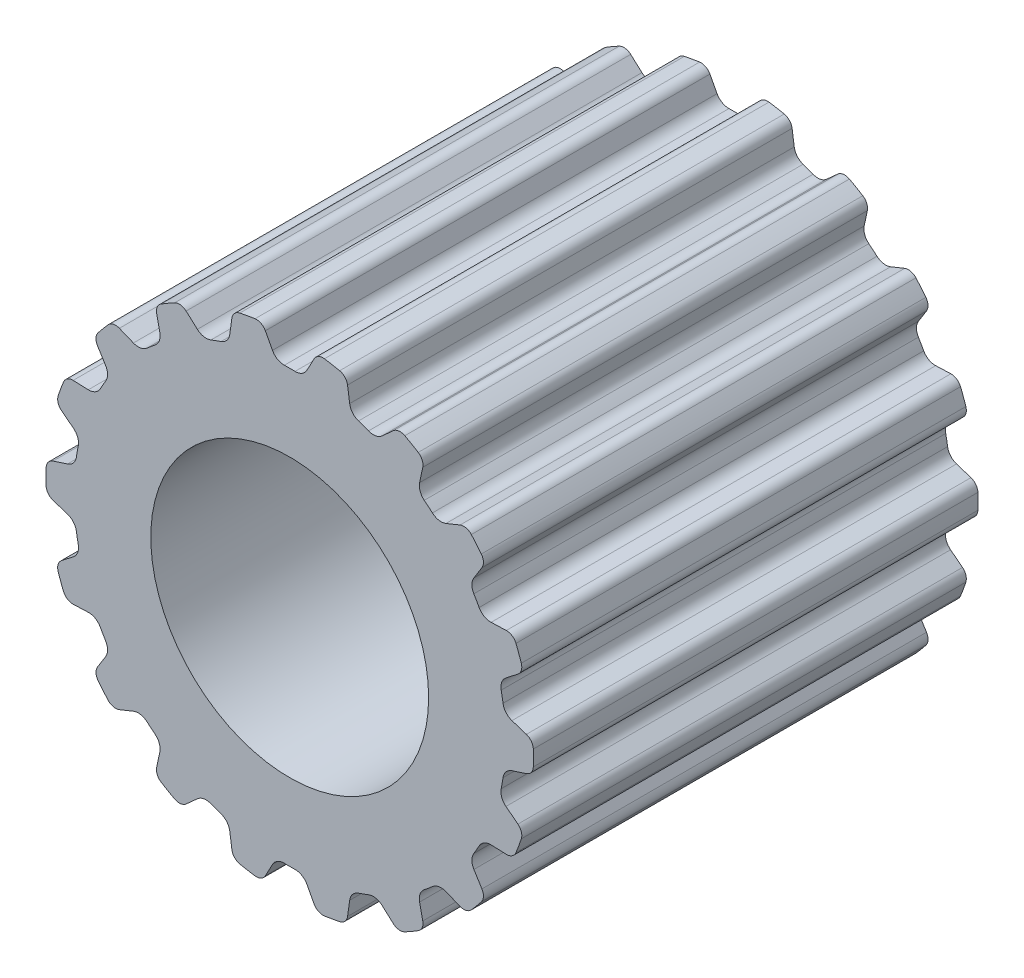
SolidWorks part; units mm, degrees
ref_plane "Front Plane" through (0, 0, 0) normal (0, 0, 1) x (1, 0, 0)
ref_plane "Top Plane" through (0, 0, 0) normal (0, 1, 0) x (1, 0, 0)
ref_plane "Right Plane" through (0, 0, 0) normal (1, 0, 0) x (0, 0, -1)
sketch "Sketch1" plane through (0, 0, 0) normal (0, 0, 1) x (1, 0, 0)
  circle A0 centre (0, 0) radius 5.57
  dimension "OD" = 11.14
sketch "PITCH DIAMETER" plane through (0, 0, 0) normal (0, 0, 1) x (1, 0, 0)
  circle A0 centre (0, 0) radius 5.82
  dimension "PD" = 11.64
extrude "Boss-Extrude1" add sketch "Sketch1" along normal mid plane 10.16
sketch "Sketch2" plane through (0, 0, 5.08) normal (0, 0, 1) x (1, 0, 0)
  line L0 (0.305, 4.9206) -> (0.6312, 5.5341)
  line L1 (-0.305, 4.9206) -> (-0.6312, 5.5341)
  arc A0 (0.305, 4.9206) -> (-0.305, 4.9206) centre (0, 0) ccw
  circle A1 centre (0, 0) radius 5.57 construction
  arc A2 (-0.6312, 5.5341) -> (0.6312, 5.5341) centre (0, 0) cw
  dimension "D2" = 0.64
  dimension "Angle" = 56
  dimension "width" = 0.61
extrude "Cut-Extrude1" cut sketch "Sketch2" against normal through all
fillet "Fillet1" radius 0.23 2 edges at (0.6312, 5.5341, 0) (-0.6312, 5.5341, 0)
fillet "Fillet2" radius 0.3 2 edges at (0.305, 4.9206, 0) (-0.305, 4.9206, 0)
pattern_circular "CirPattern1" count 18 over 360 about axis through (0, 0, 0) along (0, 0, 1) of "Cut-Extrude1", "Fillet1", "Fillet2"
sketch "Sketch3" plane through (0, 0, 5.08) normal (0, 0, 1) x (1, 0, 0)
  circle A0 centre (0, 0) radius 3.175
  dimension "D1" = 6.35
extrude "Cut-Extrude2" cut sketch "Sketch3" against normal through all
sketch "Sketch4" plane through (0, 0, 5.08) normal (0, 0, 1) x (1, 0, 0)
  line L0 (-5.2151, -1.4847) -> (-4.9419, -1.2713)
  line L1 (-5.2151, -1.4847) -> (-4.9419, -1.2713)
  line L2 (-5.0787, -0.4956) -> (-5.4084, -0.3885)
  line L3 (-5.0787, -0.4956) -> (-5.4084, -0.3885)
  line L4 (-5.4084, 0.3885) -> (-5.0787, 0.4956)
  line L5 (-5.4084, 0.3885) -> (-5.0787, 0.4956)
  line L6 (-4.9419, 1.2713) -> (-5.2151, 1.4847)
  line L7 (-4.9419, 1.2713) -> (-5.2151, 1.4847)
  line L8 (-4.9493, 2.2148) -> (-4.6029, 2.2027)
  line L9 (-4.9493, 2.2148) -> (-4.6029, 2.2027)
  line L10 (-4.2091, 2.8848) -> (-4.3928, 3.1788)
  line L11 (-4.2091, 2.8848) -> (-4.3928, 3.1788)
  line L12 (-3.8933, 3.774) -> (-3.5719, 3.6442)
  line L13 (-3.8933, 3.774) -> (-3.5719, 3.6442)
  line L14 (-2.9686, 4.1504) -> (-3.0406, 4.4895)
  line L15 (-2.9686, 4.1504) -> (-3.0406, 4.4895)
  line L16 (-2.3677, 4.878) -> (-2.1101, 4.6461)
  line L17 (-2.3677, 4.878) -> (-2.1101, 4.6461)
  line L18 (-1.37, 4.9154) -> (-1.3217, 5.2587)
  line L19 (-1.37, 4.9154) -> (-1.3217, 5.2587)
  line L20 (-0.5566, 5.3937) -> (-0.3938, 5.0876)
  line L21 (-0.5566, 5.3937) -> (-0.3938, 5.0876)
  line L22 (0.3938, 5.0876) -> (0.5566, 5.3937)
  line L23 (0.3938, 5.0876) -> (0.5566, 5.3937)
  line L24 (1.3217, 5.2587) -> (1.37, 4.9154)
  line L25 (1.3217, 5.2587) -> (1.37, 4.9154)
  line L26 (2.1101, 4.6461) -> (2.3677, 4.878)
  line L27 (2.1101, 4.6461) -> (2.3677, 4.878)
  line L28 (3.0406, 4.4895) -> (2.9686, 4.1504)
  line L29 (3.0406, 4.4895) -> (2.9686, 4.1504)
  line L30 (3.5719, 3.6442) -> (3.8933, 3.774)
  line L31 (3.5719, 3.6442) -> (3.8933, 3.774)
  line L32 (4.3928, 3.1788) -> (4.2091, 2.8848)
  line L33 (4.3928, 3.1788) -> (4.2091, 2.8848)
  line L34 (4.6029, 2.2027) -> (4.9493, 2.2148)
  line L35 (4.6029, 2.2027) -> (4.9493, 2.2148)
  line L36 (5.2151, 1.4847) -> (4.9419, 1.2713)
  line L37 (5.2151, 1.4847) -> (4.9419, 1.2713)
  line L38 (5.0787, 0.4956) -> (5.4084, 0.3885)
  line L39 (5.0787, 0.4956) -> (5.4084, 0.3885)
  line L40 (5.4084, -0.3885) -> (5.0787, -0.4956)
  line L41 (5.4084, -0.3885) -> (5.0787, -0.4956)
  line L42 (4.9419, -1.2713) -> (5.2151, -1.4847)
  line L43 (4.9419, -1.2713) -> (5.2151, -1.4847)
  line L44 (4.9493, -2.2148) -> (4.6029, -2.2027)
  line L45 (4.9493, -2.2148) -> (4.6029, -2.2027)
  line L46 (4.2091, -2.8848) -> (4.3928, -3.1788)
  line L47 (4.2091, -2.8848) -> (4.3928, -3.1788)
  line L48 (3.8933, -3.774) -> (3.5719, -3.6442)
  line L49 (3.8933, -3.774) -> (3.5719, -3.6442)
  line L50 (2.9686, -4.1504) -> (3.0406, -4.4895)
  line L51 (2.9686, -4.1504) -> (3.0406, -4.4895)
  line L52 (2.3677, -4.878) -> (2.1101, -4.6461)
  line L53 (2.3677, -4.878) -> (2.1101, -4.6461)
  line L54 (1.37, -4.9154) -> (1.3217, -5.2587)
  line L55 (1.37, -4.9154) -> (1.3217, -5.2587)
  line L56 (0.5566, -5.3937) -> (0.3938, -5.0876)
  line L57 (0.5566, -5.3937) -> (0.3938, -5.0876)
  line L58 (-0.3938, -5.0876) -> (-0.5566, -5.3937)
  line L59 (-0.3938, -5.0876) -> (-0.5566, -5.3937)
  line L60 (-1.3217, -5.2587) -> (-1.37, -4.9154)
  line L61 (-1.3217, -5.2587) -> (-1.37, -4.9154)
  line L62 (-2.1101, -4.6461) -> (-2.3677, -4.878)
  line L63 (-2.1101, -4.6461) -> (-2.3677, -4.878)
  line L64 (-3.0406, -4.4895) -> (-2.9686, -4.1504)
  line L65 (-3.0406, -4.4895) -> (-2.9686, -4.1504)
  line L66 (-3.5719, -3.6442) -> (-3.8933, -3.774)
  line L67 (-3.5719, -3.6442) -> (-3.8933, -3.774)
  line L68 (-4.3928, -3.1788) -> (-4.2091, -2.8848)
  line L69 (-4.3928, -3.1788) -> (-4.2091, -2.8848)
  line L70 (-4.6029, -2.2027) -> (-4.9493, -2.2148)
  line L71 (-4.6029, -2.2027) -> (-4.9493, -2.2148)
  arc A0 (-5.292, -1.7377) -> (-5.1709, -2.0705) centre (0, 0) ccw
  arc A1 (-5.292, -1.7377) -> (-5.1709, -2.0705) centre (0, 0) ccw
  arc A2 (-5.2151, -1.4847) -> (-5.292, -1.7377) centre (-5.0735, -1.666) ccw
  arc A3 (-5.2151, -1.4847) -> (-5.292, -1.7377) centre (-5.0735, -1.666) ccw
  arc A4 (-4.9419, -1.2713) -> (-4.8325, -0.9755) centre (-5.1266, -1.0349) ccw
  arc A5 (-4.9419, -1.2713) -> (-4.8325, -0.9755) centre (-5.1266, -1.0349) ccw
  arc A6 (-4.8747, -0.7361) -> (-4.8325, -0.9755) centre (0, 0) ccw
  arc A7 (-4.8747, -0.7361) -> (-4.8325, -0.9755) centre (0, 0) ccw
  arc A8 (-4.8747, -0.7361) -> (-5.0787, -0.4956) centre (-5.1714, -0.7809) ccw
  arc A9 (-4.8747, -0.7361) -> (-5.0787, -0.4956) centre (-5.1714, -0.7809) ccw
  arc A10 (-5.5672, -0.1771) -> (-5.4084, -0.3885) centre (-5.3373, -0.1698) ccw
  arc A11 (-5.5672, -0.1771) -> (-5.4084, -0.3885) centre (-5.3373, -0.1698) ccw
  arc A12 (-5.5672, 0.1771) -> (-5.5672, -0.1771) centre (0, 0) ccw
  arc A13 (-5.5672, 0.1771) -> (-5.5672, -0.1771) centre (0, 0) ccw
  arc A14 (-5.4084, 0.3885) -> (-5.5672, 0.1771) centre (-5.3373, 0.1698) ccw
  arc A15 (-5.4084, 0.3885) -> (-5.5672, 0.1771) centre (-5.3373, 0.1698) ccw
  arc A16 (-5.0787, 0.4956) -> (-4.8747, 0.7361) centre (-5.1714, 0.7809) ccw
  arc A17 (-5.0787, 0.4956) -> (-4.8747, 0.7361) centre (-5.1714, 0.7809) ccw
  arc A18 (-4.8325, 0.9755) -> (-4.8747, 0.7361) centre (0, 0) ccw
  arc A19 (-4.8325, 0.9755) -> (-4.8747, 0.7361) centre (0, 0) ccw
  arc A20 (-4.8325, 0.9755) -> (-4.9419, 1.2713) centre (-5.1266, 1.0349) ccw
  arc A21 (-4.8325, 0.9755) -> (-4.9419, 1.2713) centre (-5.1266, 1.0349) ccw
  arc A22 (-5.292, 1.7377) -> (-5.2151, 1.4847) centre (-5.0735, 1.666) ccw
  arc A23 (-5.292, 1.7377) -> (-5.2151, 1.4847) centre (-5.0735, 1.666) ccw
  arc A24 (-5.1709, 2.0705) -> (-5.292, 1.7377) centre (0, 0) ccw
  arc A25 (-5.1709, 2.0705) -> (-5.292, 1.7377) centre (0, 0) ccw
  arc A26 (-4.9493, 2.2148) -> (-5.1709, 2.0705) centre (-4.9574, 1.985) ccw
  arc A27 (-4.9493, 2.2148) -> (-5.1709, 2.0705) centre (-4.9574, 1.985) ccw
  arc A28 (-4.6029, 2.2027) -> (-4.329, 2.359) centre (-4.5924, 2.5026) ccw
  arc A29 (-4.6029, 2.2027) -> (-4.329, 2.359) centre (-4.5924, 2.5026) ccw
  arc A30 (-4.2074, 2.5695) -> (-4.329, 2.359) centre (0, 0) ccw
  arc A31 (-4.2074, 2.5695) -> (-4.329, 2.359) centre (0, 0) ccw
  arc A32 (-4.2074, 2.5695) -> (-4.2091, 2.8848) centre (-4.4635, 2.7259) ccw
  arc A33 (-4.2074, 2.5695) -> (-4.2091, 2.8848) centre (-4.4635, 2.7259) ccw
  arc A34 (-4.3785, 3.4429) -> (-4.3928, 3.1788) centre (-4.1977, 3.3007) ccw
  arc A35 (-4.3785, 3.4429) -> (-4.3928, 3.1788) centre (-4.1977, 3.3007) ccw
  arc A36 (-4.1509, 3.7142) -> (-4.3785, 3.4429) centre (0, 0) ccw
  arc A37 (-4.1509, 3.7142) -> (-4.3785, 3.4429) centre (0, 0) ccw
  arc A38 (-3.8933, 3.774) -> (-4.1509, 3.7142) centre (-3.9795, 3.5608) ccw
  arc A39 (-3.8933, 3.774) -> (-4.1509, 3.7142) centre (-3.9795, 3.5608) ccw
  arc A40 (-3.5719, 3.6442) -> (-3.2611, 3.6973) centre (-3.4595, 3.9223) ccw
  arc A41 (-3.5719, 3.6442) -> (-3.2611, 3.6973) centre (-3.4595, 3.9223) ccw
  arc A42 (-3.0749, 3.8536) -> (-3.2611, 3.6973) centre (0, 0) ccw
  arc A43 (-3.0749, 3.8536) -> (-3.2611, 3.6973) centre (0, 0) ccw
  arc A44 (-3.0749, 3.8536) -> (-2.9686, 4.1504) centre (-3.262, 4.0881) ccw
  arc A45 (-3.0749, 3.8536) -> (-2.9686, 4.1504) centre (-3.262, 4.0881) ccw
  arc A46 (-2.9369, 4.7328) -> (-3.0406, 4.4895) centre (-2.8157, 4.5374) ccw
  arc A47 (-2.9369, 4.7328) -> (-3.0406, 4.4895) centre (-2.8157, 4.5374) ccw
  arc A48 (-2.6303, 4.9099) -> (-2.9369, 4.7328) centre (0, 0) ccw
  arc A49 (-2.6303, 4.9099) -> (-2.9369, 4.7328) centre (0, 0) ccw
  arc A50 (-2.3677, 4.878) -> (-2.6303, 4.9099) centre (-2.5216, 4.7071) ccw
  arc A51 (-2.3677, 4.878) -> (-2.6303, 4.9099) centre (-2.5216, 4.7071) ccw
  arc A52 (-2.1101, 4.6461) -> (-1.7998, 4.5897) centre (-1.9094, 4.869) ccw
  arc A53 (-2.1101, 4.6461) -> (-1.7998, 4.5897) centre (-1.9094, 4.869) ccw
  arc A54 (-1.5714, 4.6728) -> (-1.7998, 4.5897) centre (0, 0) ccw
  arc A55 (-1.5714, 4.6728) -> (-1.7998, 4.5897) centre (0, 0) ccw
  arc A56 (-1.5714, 4.6728) -> (-1.37, 4.9154) centre (-1.6671, 4.9572) ccw
  arc A57 (-1.5714, 4.6728) -> (-1.37, 4.9154) centre (-1.6671, 4.9572) ccw
  arc A58 (-1.1411, 5.4519) -> (-1.3217, 5.2587) centre (-1.094, 5.2267) ccw
  arc A59 (-1.1411, 5.4519) -> (-1.3217, 5.2587) centre (-1.094, 5.2267) ccw
  arc A60 (-0.7924, 5.5134) -> (-1.1411, 5.4519) centre (0, 0) ccw
  arc A61 (-0.7924, 5.5134) -> (-1.1411, 5.4519) centre (0, 0) ccw
  arc A62 (-0.5566, 5.3937) -> (-0.7924, 5.5134) centre (-0.7596, 5.2857) ccw
  arc A63 (-0.5566, 5.3937) -> (-0.7924, 5.5134) centre (-0.7596, 5.2857) ccw
  arc A64 (-0.3938, 5.0876) -> (-0.1215, 4.9285) centre (-0.1289, 5.2284) ccw
  arc A65 (-0.3938, 5.0876) -> (-0.1215, 4.9285) centre (-0.1289, 5.2284) ccw
  arc A66 (0.1215, 4.9285) -> (-0.1215, 4.9285) centre (0, 0) ccw
  arc A67 (0.1215, 4.9285) -> (-0.1215, 4.9285) centre (0, 0) ccw
  arc A68 (0.1215, 4.9285) -> (0.3938, 5.0876) centre (0.1289, 5.2284) ccw
  arc A69 (0.1215, 4.9285) -> (0.3938, 5.0876) centre (0.1289, 5.2284) ccw
  arc A70 (0.7924, 5.5134) -> (0.5566, 5.3937) centre (0.7596, 5.2857) ccw
  arc A71 (0.7924, 5.5134) -> (0.5566, 5.3937) centre (0.7596, 5.2857) ccw
  arc A72 (1.1411, 5.4519) -> (0.7924, 5.5134) centre (0, 0) ccw
  arc A73 (1.1411, 5.4519) -> (0.7924, 5.5134) centre (0, 0) ccw
  arc A74 (1.3217, 5.2587) -> (1.1411, 5.4519) centre (1.094, 5.2267) ccw
  arc A75 (1.3217, 5.2587) -> (1.1411, 5.4519) centre (1.094, 5.2267) ccw
  arc A76 (1.37, 4.9154) -> (1.5714, 4.6728) centre (1.6671, 4.9572) ccw
  arc A77 (1.37, 4.9154) -> (1.5714, 4.6728) centre (1.6671, 4.9572) ccw
  arc A78 (1.7998, 4.5897) -> (1.5714, 4.6728) centre (0, 0) ccw
  arc A79 (1.7998, 4.5897) -> (1.5714, 4.6728) centre (0, 0) ccw
  arc A80 (1.7998, 4.5897) -> (2.1101, 4.6461) centre (1.9094, 4.869) ccw
  arc A81 (1.7998, 4.5897) -> (2.1101, 4.6461) centre (1.9094, 4.869) ccw
  arc A82 (2.6303, 4.9099) -> (2.3677, 4.878) centre (2.5216, 4.7071) ccw
  arc A83 (2.6303, 4.9099) -> (2.3677, 4.878) centre (2.5216, 4.7071) ccw
  arc A84 (2.9369, 4.7328) -> (2.6303, 4.9099) centre (0, 0) ccw
  arc A85 (2.9369, 4.7328) -> (2.6303, 4.9099) centre (0, 0) ccw
  arc A86 (3.0406, 4.4895) -> (2.9369, 4.7328) centre (2.8157, 4.5374) ccw
  arc A87 (3.0406, 4.4895) -> (2.9369, 4.7328) centre (2.8157, 4.5374) ccw
  arc A88 (2.9686, 4.1504) -> (3.0749, 3.8536) centre (3.262, 4.0881) ccw
  arc A89 (2.9686, 4.1504) -> (3.0749, 3.8536) centre (3.262, 4.0881) ccw
  arc A90 (3.2611, 3.6973) -> (3.0749, 3.8536) centre (0, 0) ccw
  arc A91 (3.2611, 3.6973) -> (3.0749, 3.8536) centre (0, 0) ccw
  arc A92 (3.2611, 3.6973) -> (3.5719, 3.6442) centre (3.4595, 3.9223) ccw
  arc A93 (3.2611, 3.6973) -> (3.5719, 3.6442) centre (3.4595, 3.9223) ccw
  arc A94 (4.1509, 3.7142) -> (3.8933, 3.774) centre (3.9795, 3.5608) ccw
  arc A95 (4.1509, 3.7142) -> (3.8933, 3.774) centre (3.9795, 3.5608) ccw
  arc A96 (4.3785, 3.4429) -> (4.1509, 3.7142) centre (0, 0) ccw
  arc A97 (4.3785, 3.4429) -> (4.1509, 3.7142) centre (0, 0) ccw
  arc A98 (4.3928, 3.1788) -> (4.3785, 3.4429) centre (4.1977, 3.3007) ccw
  arc A99 (4.3928, 3.1788) -> (4.3785, 3.4429) centre (4.1977, 3.3007) ccw
  arc A100 (4.2091, 2.8848) -> (4.2074, 2.5695) centre (4.4635, 2.7259) ccw
  arc A101 (4.2091, 2.8848) -> (4.2074, 2.5695) centre (4.4635, 2.7259) ccw
  arc A102 (4.329, 2.359) -> (4.2074, 2.5695) centre (0, 0) ccw
  arc A103 (4.329, 2.359) -> (4.2074, 2.5695) centre (0, 0) ccw
  arc A104 (4.329, 2.359) -> (4.6029, 2.2027) centre (4.5924, 2.5026) ccw
  arc A105 (4.329, 2.359) -> (4.6029, 2.2027) centre (4.5924, 2.5026) ccw
  arc A106 (5.1709, 2.0705) -> (4.9493, 2.2148) centre (4.9574, 1.985) ccw
  arc A107 (5.1709, 2.0705) -> (4.9493, 2.2148) centre (4.9574, 1.985) ccw
  arc A108 (5.292, 1.7377) -> (5.1709, 2.0705) centre (0, 0) ccw
  arc A109 (5.292, 1.7377) -> (5.1709, 2.0705) centre (0, 0) ccw
  arc A110 (5.2151, 1.4847) -> (5.292, 1.7377) centre (5.0735, 1.666) ccw
  arc A111 (5.2151, 1.4847) -> (5.292, 1.7377) centre (5.0735, 1.666) ccw
  arc A112 (4.9419, 1.2713) -> (4.8325, 0.9755) centre (5.1266, 1.0349) ccw
  arc A113 (4.9419, 1.2713) -> (4.8325, 0.9755) centre (5.1266, 1.0349) ccw
  arc A114 (4.8747, 0.7361) -> (4.8325, 0.9755) centre (0, 0) ccw
  arc A115 (4.8747, 0.7361) -> (4.8325, 0.9755) centre (0, 0) ccw
  arc A116 (4.8747, 0.7361) -> (5.0787, 0.4956) centre (5.1714, 0.7809) ccw
  arc A117 (4.8747, 0.7361) -> (5.0787, 0.4956) centre (5.1714, 0.7809) ccw
  arc A118 (5.5672, 0.1771) -> (5.4084, 0.3885) centre (5.3373, 0.1698) ccw
  arc A119 (5.5672, 0.1771) -> (5.4084, 0.3885) centre (5.3373, 0.1698) ccw
  arc A120 (5.5672, -0.1771) -> (5.5672, 0.1771) centre (0, 0) ccw
  arc A121 (5.5672, -0.1771) -> (5.5672, 0.1771) centre (0, 0) ccw
  arc A122 (5.4084, -0.3885) -> (5.5672, -0.1771) centre (5.3373, -0.1698) ccw
  arc A123 (5.4084, -0.3885) -> (5.5672, -0.1771) centre (5.3373, -0.1698) ccw
  arc A124 (5.0787, -0.4956) -> (4.8747, -0.7361) centre (5.1714, -0.7809) ccw
  arc A125 (5.0787, -0.4956) -> (4.8747, -0.7361) centre (5.1714, -0.7809) ccw
  arc A126 (4.8325, -0.9755) -> (4.8747, -0.7361) centre (0, 0) ccw
  arc A127 (4.8325, -0.9755) -> (4.8747, -0.7361) centre (0, 0) ccw
  arc A128 (4.8325, -0.9755) -> (4.9419, -1.2713) centre (5.1266, -1.0349) ccw
  arc A129 (4.8325, -0.9755) -> (4.9419, -1.2713) centre (5.1266, -1.0349) ccw
  arc A130 (5.292, -1.7377) -> (5.2151, -1.4847) centre (5.0735, -1.666) ccw
  arc A131 (5.292, -1.7377) -> (5.2151, -1.4847) centre (5.0735, -1.666) ccw
  arc A132 (5.1709, -2.0705) -> (5.292, -1.7377) centre (0, 0) ccw
  arc A133 (5.1709, -2.0705) -> (5.292, -1.7377) centre (0, 0) ccw
  arc A134 (4.9493, -2.2148) -> (5.1709, -2.0705) centre (4.9574, -1.985) ccw
  arc A135 (4.9493, -2.2148) -> (5.1709, -2.0705) centre (4.9574, -1.985) ccw
  arc A136 (4.6029, -2.2027) -> (4.329, -2.359) centre (4.5924, -2.5026) ccw
  arc A137 (4.6029, -2.2027) -> (4.329, -2.359) centre (4.5924, -2.5026) ccw
  arc A138 (4.2074, -2.5695) -> (4.329, -2.359) centre (0, 0) ccw
  arc A139 (4.2074, -2.5695) -> (4.329, -2.359) centre (0, 0) ccw
  arc A140 (4.2074, -2.5695) -> (4.2091, -2.8848) centre (4.4635, -2.7259) ccw
  arc A141 (4.2074, -2.5695) -> (4.2091, -2.8848) centre (4.4635, -2.7259) ccw
  arc A142 (4.3785, -3.4429) -> (4.3928, -3.1788) centre (4.1977, -3.3007) ccw
  arc A143 (4.3785, -3.4429) -> (4.3928, -3.1788) centre (4.1977, -3.3007) ccw
  arc A144 (4.1509, -3.7142) -> (4.3785, -3.4429) centre (0, 0) ccw
  arc A145 (4.1509, -3.7142) -> (4.3785, -3.4429) centre (0, 0) ccw
  arc A146 (3.8933, -3.774) -> (4.1509, -3.7142) centre (3.9795, -3.5608) ccw
  arc A147 (3.8933, -3.774) -> (4.1509, -3.7142) centre (3.9795, -3.5608) ccw
  arc A148 (3.5719, -3.6442) -> (3.2611, -3.6973) centre (3.4595, -3.9223) ccw
  arc A149 (3.5719, -3.6442) -> (3.2611, -3.6973) centre (3.4595, -3.9223) ccw
  arc A150 (3.0749, -3.8536) -> (3.2611, -3.6973) centre (0, 0) ccw
  arc A151 (3.0749, -3.8536) -> (3.2611, -3.6973) centre (0, 0) ccw
  arc A152 (3.0749, -3.8536) -> (2.9686, -4.1504) centre (3.262, -4.0881) ccw
  arc A153 (3.0749, -3.8536) -> (2.9686, -4.1504) centre (3.262, -4.0881) ccw
  arc A154 (2.9369, -4.7328) -> (3.0406, -4.4895) centre (2.8157, -4.5374) ccw
  arc A155 (2.9369, -4.7328) -> (3.0406, -4.4895) centre (2.8157, -4.5374) ccw
  arc A156 (2.6303, -4.9099) -> (2.9369, -4.7328) centre (0, 0) ccw
  arc A157 (2.6303, -4.9099) -> (2.9369, -4.7328) centre (0, 0) ccw
  arc A158 (2.3677, -4.878) -> (2.6303, -4.9099) centre (2.5216, -4.7071) ccw
  arc A159 (2.3677, -4.878) -> (2.6303, -4.9099) centre (2.5216, -4.7071) ccw
  arc A160 (2.1101, -4.6461) -> (1.7998, -4.5897) centre (1.9094, -4.869) ccw
  arc A161 (2.1101, -4.6461) -> (1.7998, -4.5897) centre (1.9094, -4.869) ccw
  arc A162 (1.5714, -4.6728) -> (1.7998, -4.5897) centre (0, 0) ccw
  arc A163 (1.5714, -4.6728) -> (1.7998, -4.5897) centre (0, 0) ccw
  arc A164 (1.5714, -4.6728) -> (1.37, -4.9154) centre (1.6671, -4.9572) ccw
  arc A165 (1.5714, -4.6728) -> (1.37, -4.9154) centre (1.6671, -4.9572) ccw
  arc A166 (1.1411, -5.4519) -> (1.3217, -5.2587) centre (1.094, -5.2267) ccw
  arc A167 (1.1411, -5.4519) -> (1.3217, -5.2587) centre (1.094, -5.2267) ccw
  arc A168 (0.7924, -5.5134) -> (1.1411, -5.4519) centre (0, 0) ccw
  arc A169 (0.7924, -5.5134) -> (1.1411, -5.4519) centre (0, 0) ccw
  arc A170 (0.5566, -5.3937) -> (0.7924, -5.5134) centre (0.7596, -5.2857) ccw
  arc A171 (0.5566, -5.3937) -> (0.7924, -5.5134) centre (0.7596, -5.2857) ccw
  arc A172 (0.3938, -5.0876) -> (0.1215, -4.9285) centre (0.1289, -5.2284) ccw
  arc A173 (0.3938, -5.0876) -> (0.1215, -4.9285) centre (0.1289, -5.2284) ccw
  arc A174 (-0.1215, -4.9285) -> (0.1215, -4.9285) centre (0, 0) ccw
  arc A175 (-0.1215, -4.9285) -> (0.1215, -4.9285) centre (0, 0) ccw
  arc A176 (-0.1215, -4.9285) -> (-0.3938, -5.0876) centre (-0.1289, -5.2284) ccw
  arc A177 (-0.1215, -4.9285) -> (-0.3938, -5.0876) centre (-0.1289, -5.2284) ccw
  arc A178 (-0.7924, -5.5134) -> (-0.5566, -5.3937) centre (-0.7596, -5.2857) ccw
  arc A179 (-0.7924, -5.5134) -> (-0.5566, -5.3937) centre (-0.7596, -5.2857) ccw
  arc A180 (-1.1411, -5.4519) -> (-0.7924, -5.5134) centre (0, 0) ccw
  arc A181 (-1.1411, -5.4519) -> (-0.7924, -5.5134) centre (0, 0) ccw
  arc A182 (-1.3217, -5.2587) -> (-1.1411, -5.4519) centre (-1.094, -5.2267) ccw
  arc A183 (-1.3217, -5.2587) -> (-1.1411, -5.4519) centre (-1.094, -5.2267) ccw
  arc A184 (-1.37, -4.9154) -> (-1.5714, -4.6728) centre (-1.6671, -4.9572) ccw
  arc A185 (-1.37, -4.9154) -> (-1.5714, -4.6728) centre (-1.6671, -4.9572) ccw
  arc A186 (-1.7998, -4.5897) -> (-1.5714, -4.6728) centre (0, 0) ccw
  arc A187 (-1.7998, -4.5897) -> (-1.5714, -4.6728) centre (0, 0) ccw
  arc A188 (-1.7998, -4.5897) -> (-2.1101, -4.6461) centre (-1.9094, -4.869) ccw
  arc A189 (-1.7998, -4.5897) -> (-2.1101, -4.6461) centre (-1.9094, -4.869) ccw
  arc A190 (-2.6303, -4.9099) -> (-2.3677, -4.878) centre (-2.5216, -4.7071) ccw
  arc A191 (-2.6303, -4.9099) -> (-2.3677, -4.878) centre (-2.5216, -4.7071) ccw
  arc A192 (-2.9369, -4.7328) -> (-2.6303, -4.9099) centre (0, 0) ccw
  arc A193 (-2.9369, -4.7328) -> (-2.6303, -4.9099) centre (0, 0) ccw
  arc A194 (-3.0406, -4.4895) -> (-2.9369, -4.7328) centre (-2.8157, -4.5374) ccw
  arc A195 (-3.0406, -4.4895) -> (-2.9369, -4.7328) centre (-2.8157, -4.5374) ccw
  arc A196 (-2.9686, -4.1504) -> (-3.0749, -3.8536) centre (-3.262, -4.0881) ccw
  arc A197 (-2.9686, -4.1504) -> (-3.0749, -3.8536) centre (-3.262, -4.0881) ccw
  arc A198 (-3.2611, -3.6973) -> (-3.0749, -3.8536) centre (0, 0) ccw
  arc A199 (-3.2611, -3.6973) -> (-3.0749, -3.8536) centre (0, 0) ccw
  arc A200 (-3.2611, -3.6973) -> (-3.5719, -3.6442) centre (-3.4595, -3.9223) ccw
  arc A201 (-3.2611, -3.6973) -> (-3.5719, -3.6442) centre (-3.4595, -3.9223) ccw
  arc A202 (-4.1509, -3.7142) -> (-3.8933, -3.774) centre (-3.9795, -3.5608) ccw
  arc A203 (-4.1509, -3.7142) -> (-3.8933, -3.774) centre (-3.9795, -3.5608) ccw
  arc A204 (-4.3785, -3.4429) -> (-4.1509, -3.7142) centre (0, 0) ccw
  arc A205 (-4.3785, -3.4429) -> (-4.1509, -3.7142) centre (0, 0) ccw
  arc A206 (-4.3928, -3.1788) -> (-4.3785, -3.4429) centre (-4.1977, -3.3007) ccw
  arc A207 (-4.3928, -3.1788) -> (-4.3785, -3.4429) centre (-4.1977, -3.3007) ccw
  arc A208 (-4.2091, -2.8848) -> (-4.2074, -2.5695) centre (-4.4635, -2.7259) ccw
  arc A209 (-4.2091, -2.8848) -> (-4.2074, -2.5695) centre (-4.4635, -2.7259) ccw
  arc A210 (-4.329, -2.359) -> (-4.2074, -2.5695) centre (0, 0) ccw
  arc A211 (-4.329, -2.359) -> (-4.2074, -2.5695) centre (0, 0) ccw
  arc A212 (-4.329, -2.359) -> (-4.6029, -2.2027) centre (-4.5924, -2.5026) ccw
  arc A213 (-4.329, -2.359) -> (-4.6029, -2.2027) centre (-4.5924, -2.5026) ccw
  arc A214 (-5.1709, -2.0705) -> (-4.9493, -2.2148) centre (-4.9574, -1.985) ccw
  arc A215 (-5.1709, -2.0705) -> (-4.9493, -2.2148) centre (-4.9574, -1.985) ccw
